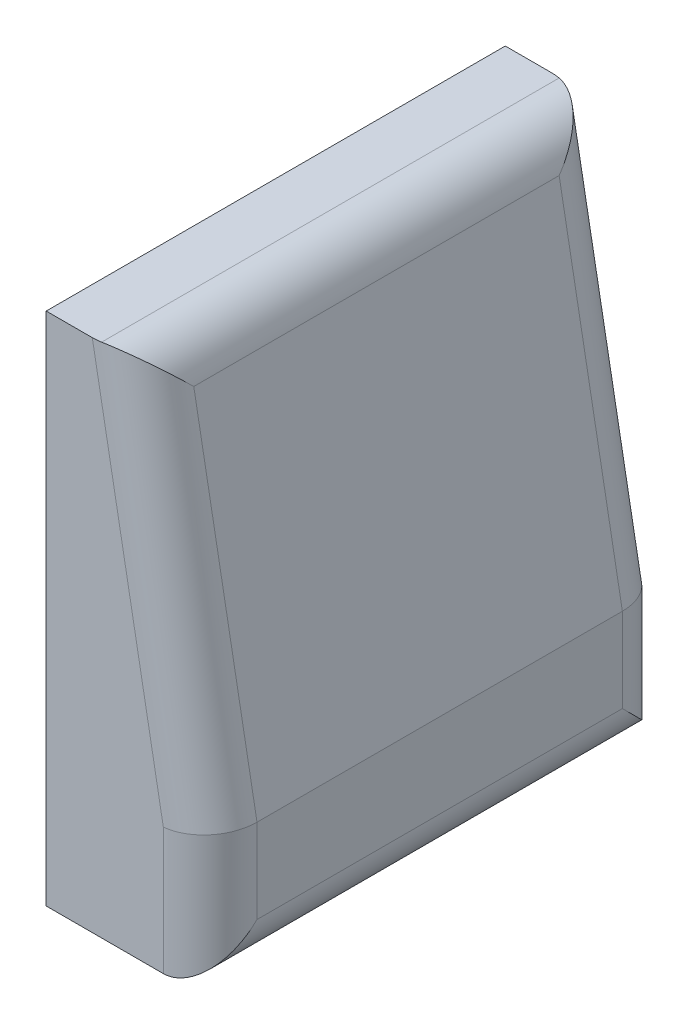
SolidWorks part; units mm, degrees
ref_plane "Front Plane" through (0, 0, 0) normal (0, 0, 1) x (1, 0, 0)
ref_plane "Top Plane" through (0, 0, 0) normal (0, 1, 0) x (1, 0, 0)
ref_plane "Right Plane" through (0, 0, 0) normal (1, 0, 0) x (0, 0, -1)
sketch "Sketch1" plane through (0, 0, 0) normal (0, 0, 1) x (1, 0, 0)
  line L0 (0, 550) -> (0, -550)
  line L1 (0, -550) -> (350, -550)
  line L2 (350, -550) -> (350, -270)
  line L3 (350, -270) -> (200, 550)
  line L4 (200, 550) -> (0, 550)
  dimension "D1" = 1100
  dimension "D2" = 200
  dimension "D3" = 280
  dimension "D4" = 350
extrude "Boss-Extrude1" add sketch "Sketch1" along normal mid plane 980
fillet "Fillet1" radius 100 6 edges at (350, -410, -490) (350, -550, 0) (350, -410, 490) (275, 140, 490) (275, 140, -490) (200, 550, 0)
